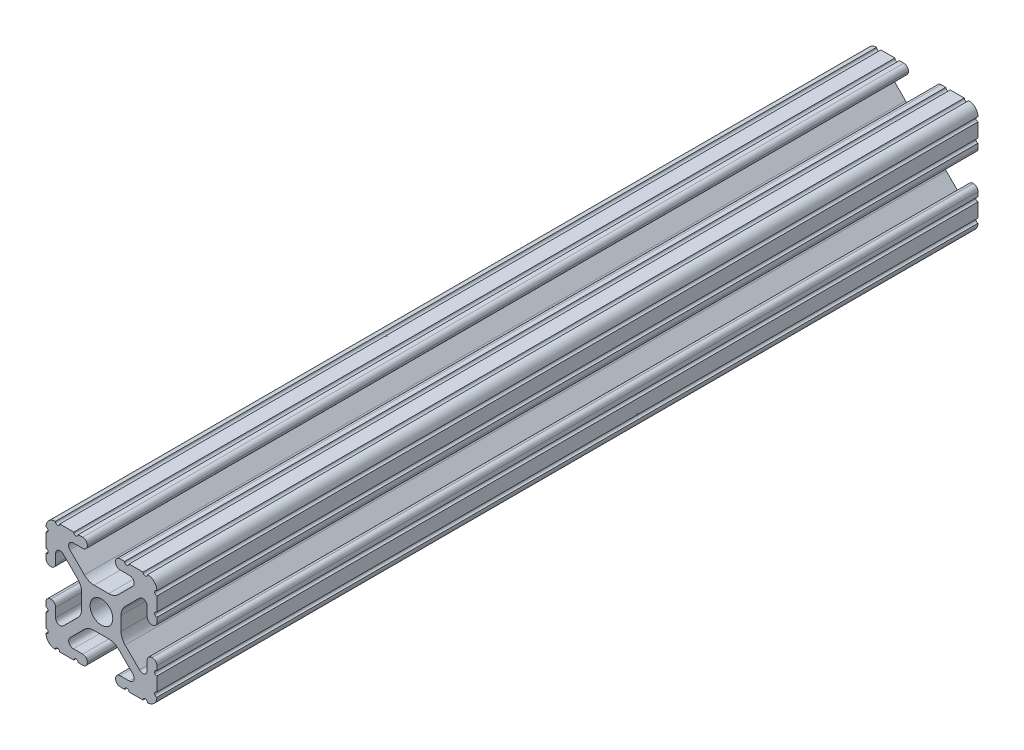
SolidWorks part; units mm, degrees
ref_plane "Front Plane" through (0, 0, 0) normal (0, 0, 1) x (1, 0, 0)
ref_plane "Top Plane" through (0, 0, 0) normal (0, 1, 0) x (1, 0, 0)
ref_plane "Right Plane" through (0, 0, 0) normal (1, 0, 0) x (0, 0, -1)
sketch "Sketch1" plane through (0, 0, 0) normal (0, 0, 1) x (1, 0, 0)
  line L88 (-7.1797, -8.6452) -> (-3.9523, -5.4237)
  line L89 (-1.7093, -4.4958) -> (1.7093, -4.4958)
  line L90 (3.9523, -5.4237) -> (7.1797, -8.6452)
  line L91 (6.4164, -10.4902) -> (4.2875, -10.4902)
  line L92 (3.2385, -11.5392) -> (3.2385, -11.651)
  line L93 (4.2875, -12.7) -> (5.3171, -12.7)
  line L94 (6.3331, -12.7) -> (9.5504, -12.7)
  line L95 (12.7, -9.5504) -> (12.7, -6.3331)
  line L96 (12.7, -5.3171) -> (12.7, -4.2875)
  line L97 (11.651, -3.2385) -> (11.5392, -3.2385)
  line L98 (10.4902, -4.2875) -> (10.4902, -6.4021)
  line L99 (8.7371, -7.1294) -> (5.441, -3.8408)
  line L100 (4.5085, -1.5932) -> (4.5085, 1.5932)
  line L101 (5.441, 3.8408) -> (8.7371, 7.1294)
  line L102 (10.4902, 6.4021) -> (10.4902, 4.2875)
  line L103 (11.5392, 3.2385) -> (11.651, 3.2385)
  line L104 (12.7, 4.2875) -> (12.7, 5.3171)
  line L105 (12.7, 6.3331) -> (12.7, 9.5504)
  line L106 (9.5504, 12.7) -> (6.3331, 12.7)
  line L107 (5.3171, 12.7) -> (4.2875, 12.7)
  line L108 (3.2385, 11.651) -> (3.2385, 11.5392)
  line L109 (4.2875, 10.4902) -> (6.4768, 10.4902)
  line L110 (7.207, 8.7244) -> (3.8983, 5.4232)
  line L111 (1.6558, 4.4958) -> (-1.6558, 4.4958)
  line L112 (-3.8983, 5.4232) -> (-7.207, 8.7244)
  line L113 (-6.4768, 10.4902) -> (-4.2875, 10.4902)
  line L114 (-3.2385, 11.5392) -> (-3.2385, 11.651)
  line L115 (-4.2875, 12.7) -> (-5.3171, 12.7)
  line L116 (-6.3331, 12.7) -> (-9.5504, 12.7)
  line L117 (-12.7, 9.5504) -> (-12.7, 6.3331)
  line L118 (-12.7, 5.3171) -> (-12.7, 4.2875)
  line L119 (-11.651, 3.2385) -> (-11.5392, 3.2385)
  line L120 (-10.4902, 4.2875) -> (-10.4902, 6.4021)
  line L121 (-8.7371, 7.1294) -> (-5.441, 3.8408)
  line L122 (-4.5085, 1.5932) -> (-4.5085, -1.5932)
  line L123 (-5.441, -3.8408) -> (-8.7371, -7.1294)
  line L124 (-10.4902, -6.4021) -> (-10.4902, -4.2875)
  line L125 (-11.5392, -3.2385) -> (-11.651, -3.2385)
  line L126 (-12.7, -4.2875) -> (-12.7, -5.3171)
  line L127 (-12.7, -6.3331) -> (-12.7, -9.5504)
  line L128 (-9.5504, -12.7) -> (-6.3331, -12.7)
  line L129 (-5.3171, -12.7) -> (-4.2875, -12.7)
  line L130 (-3.2385, -11.651) -> (-3.2385, -11.5392)
  line L131 (-4.2875, -10.4902) -> (-6.4164, -10.4902)
  circle A1 centre (0, 0) radius 2.6035
  arc A104 (-7.1797, -8.6452) -> (-6.4164, -10.4902) centre (-6.4164, -9.4098) ccw
  arc A105 (-1.7093, -4.4958) -> (-3.9523, -5.4237) centre (-1.7093, -7.6708) ccw
  arc A106 (3.9523, -5.4237) -> (1.7093, -4.4958) centre (1.7093, -7.6708) ccw
  arc A107 (6.4164, -10.4902) -> (7.1797, -8.6452) centre (6.4164, -9.4098) ccw
  arc A108 (4.2875, -10.4902) -> (3.2385, -11.5392) centre (4.2875, -11.5392) ccw
  arc A109 (3.2385, -11.651) -> (4.2875, -12.7) centre (4.2875, -11.651) ccw
  arc A110 (6.3331, -12.7) -> (5.3171, -12.7) centre (5.8251, -12.7) ccw
  arc A111 (10.5664, -12.6998) -> (9.5504, -12.7) centre (10.0584, -12.7) ccw
  arc A112 (10.5664, -12.6998) -> (12.6998, -10.5664) centre (10.5918, -10.5918) ccw
  arc A113 (12.7, -9.5504) -> (12.6998, -10.5664) centre (12.7, -10.0584) ccw
  arc A114 (12.7, -5.3171) -> (12.7, -6.3331) centre (12.7, -5.8251) ccw
  arc A115 (12.7, -4.2875) -> (11.651, -3.2385) centre (11.651, -4.2875) ccw
  arc A116 (11.5392, -3.2385) -> (10.4902, -4.2875) centre (11.5392, -4.2875) ccw
  arc A117 (8.7371, -7.1294) -> (10.4902, -6.4021) centre (9.4628, -6.4021) ccw
  arc A118 (4.5085, -1.5932) -> (5.441, -3.8408) centre (7.6835, -1.5932) ccw
  arc A119 (5.441, 3.8408) -> (4.5085, 1.5932) centre (7.6835, 1.5932) ccw
  arc A120 (10.4902, 6.4021) -> (8.7371, 7.1294) centre (9.4628, 6.4021) ccw
  arc A121 (10.4902, 4.2875) -> (11.5392, 3.2385) centre (11.5392, 4.2875) ccw
  arc A122 (11.651, 3.2385) -> (12.7, 4.2875) centre (11.651, 4.2875) ccw
  arc A123 (12.7, 6.3331) -> (12.7, 5.3171) centre (12.7, 5.8251) ccw
  arc A124 (12.6998, 10.5664) -> (12.7, 9.5504) centre (12.7, 10.0584) ccw
  arc A125 (12.6998, 10.5664) -> (10.5664, 12.6998) centre (10.5918, 10.5918) ccw
  arc A126 (9.5504, 12.7) -> (10.5664, 12.6998) centre (10.0584, 12.7) ccw
  arc A127 (5.3171, 12.7) -> (6.3331, 12.7) centre (5.8251, 12.7) ccw
  arc A128 (4.2875, 12.7) -> (3.2385, 11.651) centre (4.2875, 11.651) ccw
  arc A129 (3.2385, 11.5392) -> (4.2875, 10.4902) centre (4.2875, 11.5392) ccw
  arc A130 (7.207, 8.7244) -> (6.4768, 10.4902) centre (6.4768, 9.4563) ccw
  arc A131 (1.6558, 4.4958) -> (3.8983, 5.4232) centre (1.6558, 7.6708) ccw
  arc A132 (-3.8983, 5.4232) -> (-1.6558, 4.4958) centre (-1.6558, 7.6708) ccw
  arc A133 (-6.4768, 10.4902) -> (-7.207, 8.7244) centre (-6.4768, 9.4563) ccw
  arc A134 (-4.2875, 10.4902) -> (-3.2385, 11.5392) centre (-4.2875, 11.5392) ccw
  arc A135 (-3.2385, 11.651) -> (-4.2875, 12.7) centre (-4.2875, 11.651) ccw
  arc A136 (-6.3331, 12.7) -> (-5.3171, 12.7) centre (-5.8251, 12.7) ccw
  arc A137 (-10.5664, 12.6998) -> (-9.5504, 12.7) centre (-10.0584, 12.7) ccw
  arc A138 (-10.5664, 12.6998) -> (-12.6998, 10.5664) centre (-10.5918, 10.5918) ccw
  arc A139 (-12.7, 9.5504) -> (-12.6998, 10.5664) centre (-12.7, 10.0584) ccw
  arc A140 (-12.7, 5.3171) -> (-12.7, 6.3331) centre (-12.7, 5.8251) ccw
  arc A141 (-12.7, 4.2875) -> (-11.651, 3.2385) centre (-11.651, 4.2875) ccw
  arc A142 (-11.5392, 3.2385) -> (-10.4902, 4.2875) centre (-11.5392, 4.2875) ccw
  arc A143 (-8.7371, 7.1294) -> (-10.4902, 6.4021) centre (-9.4628, 6.4021) ccw
  arc A144 (-4.5085, 1.5932) -> (-5.441, 3.8408) centre (-7.6835, 1.5932) ccw
  arc A145 (-5.441, -3.8408) -> (-4.5085, -1.5932) centre (-7.6835, -1.5932) ccw
  arc A146 (-10.4902, -6.4021) -> (-8.7371, -7.1294) centre (-9.4628, -6.4021) ccw
  arc A147 (-10.4902, -4.2875) -> (-11.5392, -3.2385) centre (-11.5392, -4.2875) ccw
  arc A148 (-11.651, -3.2385) -> (-12.7, -4.2875) centre (-11.651, -4.2875) ccw
  arc A149 (-12.7, -6.3331) -> (-12.7, -5.3171) centre (-12.7, -5.8251) ccw
  arc A150 (-12.6998, -10.5664) -> (-12.7, -9.5504) centre (-12.7, -10.0584) ccw
  arc A151 (-12.6998, -10.5664) -> (-10.5664, -12.6998) centre (-10.5918, -10.5918) ccw
  arc A152 (-9.5504, -12.7) -> (-10.5664, -12.6998) centre (-10.0584, -12.7) ccw
  arc A153 (-5.3171, -12.7) -> (-6.3331, -12.7) centre (-5.8251, -12.7) ccw
  arc A154 (-4.2875, -12.7) -> (-3.2385, -11.651) centre (-4.2875, -11.651) ccw
  arc A155 (-3.2385, -11.5392) -> (-4.2875, -10.4902) centre (-4.2875, -11.5392) ccw
extrude "Boss-Extrude1" add sketch "Sketch1" along normal mid plane 609.6
sketch "Sketch2" plane through (12.7, 0, 0) normal (1, 0, 0) x (0, 0, -1)
  line L0 (-56.5865, 13.6438) -> (-56.5865, -14.2345) construction
  line L1 (-56.5865, -14.2345) -> (310.7431, -14.2345)
  line L2 (310.7431, -14.2345) -> (310.7431, 13.6438)
  line L3 (310.7431, 13.6438) -> (-56.5865, 13.6438)
  line L4 (-56.5865, 13.6438) -> (-101.0422, 13.6438)
  line L5 (-101.0422, 12.7) -> (-101.0422, 19.05) construction
  line L6 (-56.5865, -14.2345) -> (-101.0422, -14.2345)
  line L7 (-101.0422, -14.2345) -> (-101.0422, 13.6438)
  line L9 (-305.4758, 13.3523) -> (-289.2182, 13.3523)
  line L10 (-305.4758, 13.3523) -> (-305.4758, -14.2345)
  line L11 (-305.4758, -14.2345) -> (-289.2182, -14.2345)
  line L12 (-289.2182, 13.3523) -> (-289.2182, -14.2345)
extrude "Cut-Extrude1" cut sketch "Sketch2" against normal blind 26.162 and the other way blind 1.778
